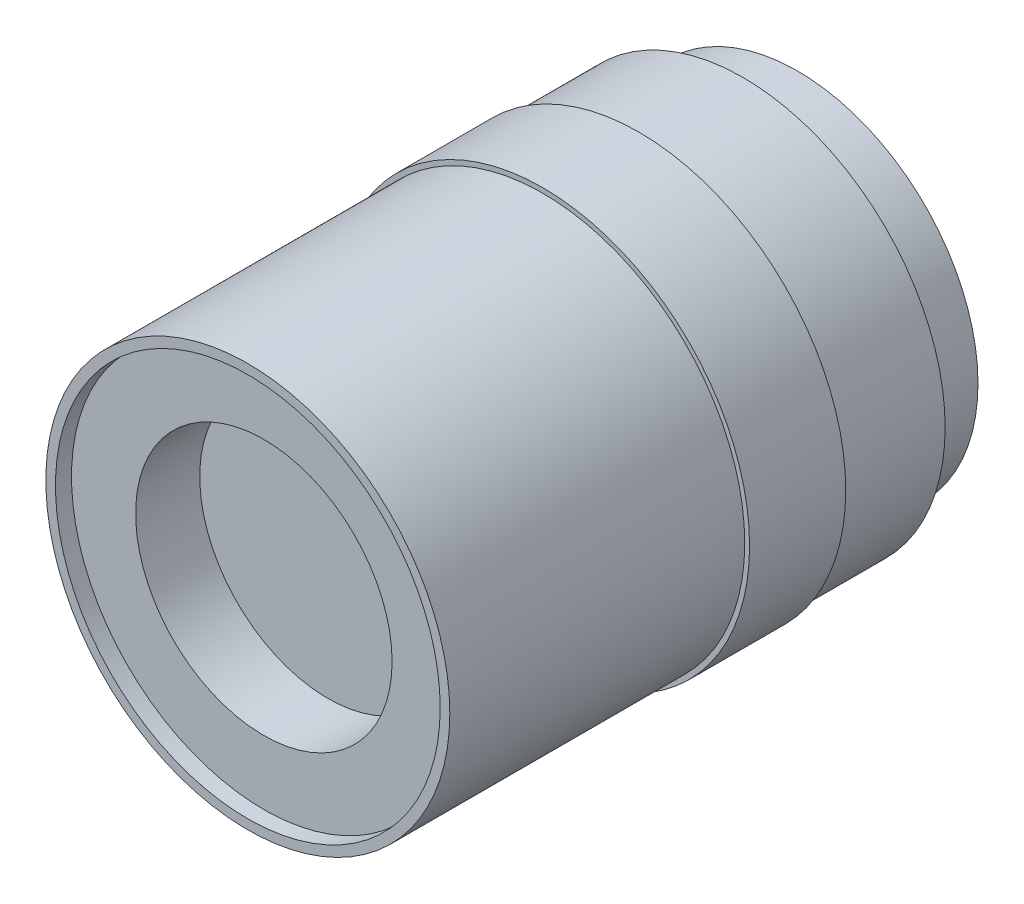
SolidWorks part; units mm, degrees
material "1060 Alloy"
ref_plane "Front Plane" through (0, 0, 0) normal (0, 0, 1) x (1, 0, 0)
ref_plane "Top Plane" through (0, 0, 0) normal (0, 1, 0) x (1, 0, 0)
ref_plane "Right Plane" through (0, 0, 0) normal (1, 0, 0) x (0, 0, -1)
sketch "Sketch1" plane through (0, 0, 0) normal (0, 0, 1) x (1, 0, 0)
  circle A0 centre (0, 0) radius 14.2875
extrude "Extrude1" add sketch "Sketch1" along normal blind 4.318
sketch "Sketch2" plane through (0, 0, 4.318) normal (0, 0, 1) x (1, 0, 0)
  circle A0 centre (0, 0) radius 16.002
extrude "Extrude2" add sketch "Sketch2" along normal blind 8.255
sketch "Sketch3" plane through (0, 0, 12.573) normal (0, 0, 1) x (1, 0, 0)
  circle A0 centre (0, 0) radius 16.383
extrude "Extrude3" add sketch "Sketch3" along normal blind 7.62
sketch "Sketch4" plane through (0, 0, 20.193) normal (0, 0, 1) x (1, 0, 0)
  circle A0 centre (0, 0) radius 16.002
extrude "Extrude4" add sketch "Sketch4" along normal blind 23.368
sketch "Sketch5" plane through (0, 0, 43.561) normal (0, 0, 1) x (1, 0, 0)
  circle A0 centre (0, 0) radius 15.24
extrude "Cut-Extrude1" cut sketch "Sketch5" against normal blind 1.27
sketch "Sketch6" plane through (0, 0, 42.291) normal (0, 0, 1) x (1, 0, 0)
  circle A0 centre (0, 0) radius 10.16
extrude "Cut-Extrude2" cut sketch "Sketch6" against normal blind 5.08
